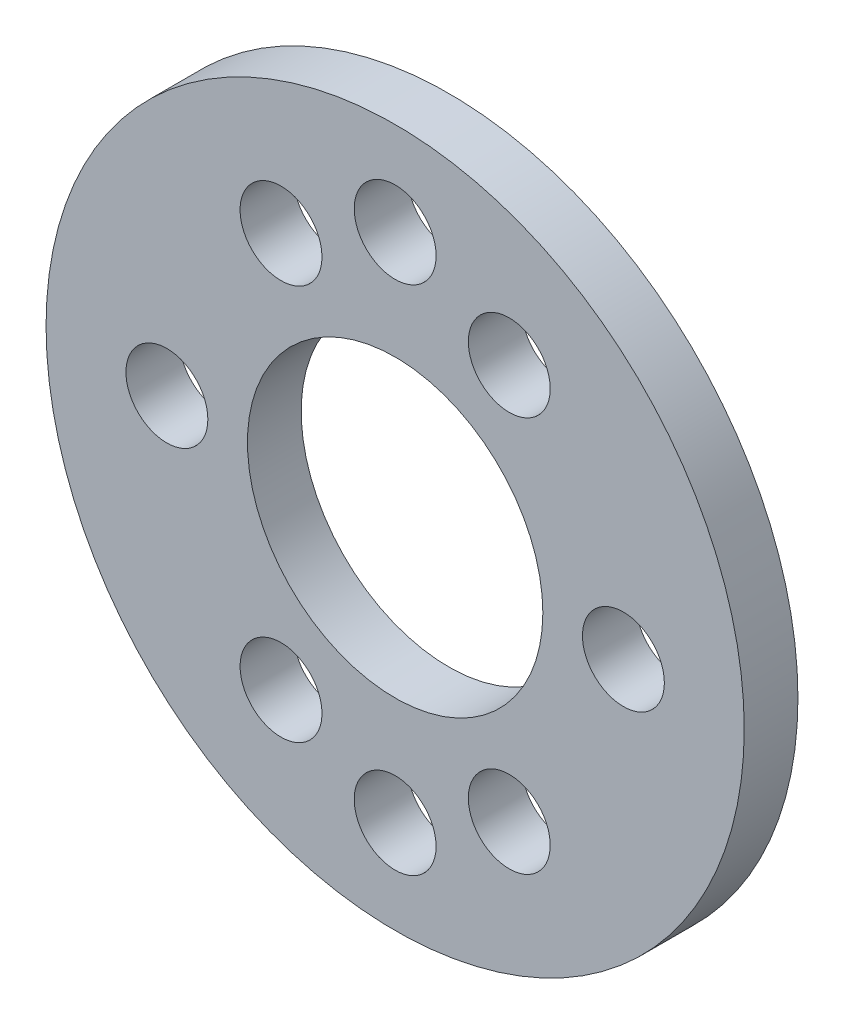
SolidWorks part; units mm, degrees
ref_plane "Front Plane" through (0, 0, 0) normal (1, 0, 0) x (0, 1, 0)
ref_plane "Top Plane" through (0, 0, 0) normal (0, 0, 1) x (0, 1, 0)
ref_plane "Right Plane" through (0, 0, 0) normal (0, 1, 0) x (-1, 0, 0)
sketch "Sketch2" plane through (0, 0, 0) normal (0, 0, 1) x (0, 1, 0)
  line L0 (0, 13) -> (0, -13) construction
  line L1 (-13, 0) -> (13, 0) construction
  line L2 (-11.2583, -6.5) -> (11.2583, 6.5) construction
  line L3 (-11.2583, 6.5) -> (11.2583, -6.5) construction
  circle A0 centre (0, 0) radius 13
  circle A1 centre (0, 0) radius 5.5
  circle A2 centre (0, 0) radius 8.5 construction
  circle A3 centre (0, 8.5) radius 1.525
  circle A4 centre (0, -8.5) radius 1.525
  circle A5 centre (7.3612, 4.25) radius 1.525
  circle A6 centre (7.3612, -4.25) radius 1.525
  circle A7 centre (-7.3612, -4.25) radius 1.525
  circle A8 centre (-7.3612, 4.25) radius 1.525
  circle A9 centre (-9.525, 0) radius 1.525
  circle A10 centre (9.525, 0) radius 1.525
  circle A11 centre (0, 0) radius 9.525 construction
  dimension "D1" = 11
  dimension "26" = 26
  dimension "D2" = 17
  dimension "D4" = 60
  dimension "D5" = 3.05
  dimension "D6" = 3.05
  dimension "D7" = 3.05
  dimension "D8" = 3.05
  dimension "D10" = 19.05
  dimension "D11" = 3.05
  dimension "D12" = 3.05
  dimension "D3" = 60
  dimension "D9" = 19.05
extrude "Boss-Extrude1" add sketch "Sketch2" along normal blind 2
